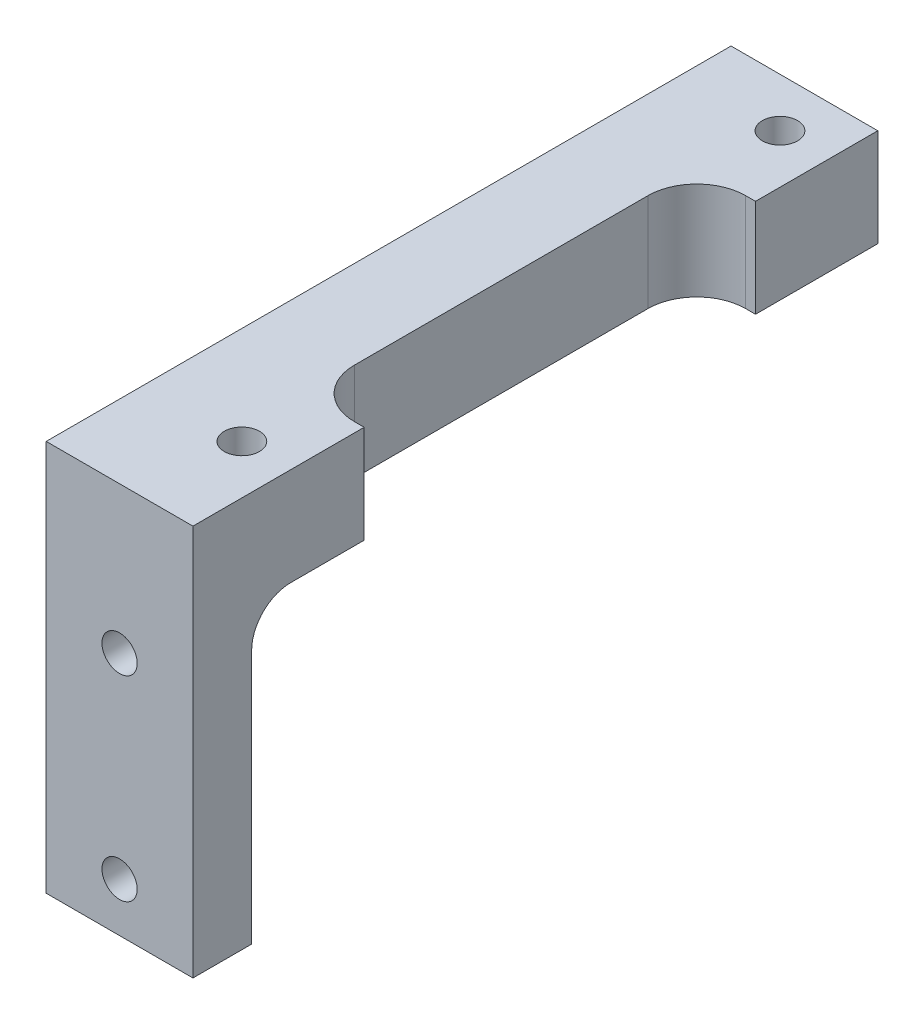
SolidWorks part; units mm, degrees
ref_plane "Front Plane" through (0, 0, 0) normal (0, 0, 1) x (1, 0, 0)
ref_plane "Top Plane" through (0, 0, 0) normal (0, 1, 0) x (1, 0, 0)
ref_plane "Right Plane" through (0, 0, 0) normal (1, 0, 0) x (0, 0, -1)
sketch "Sketch2" plane through (0, 0, 0) normal (0, 0, 1) x (1, 0, 0)
  line L1 (-23.8125, -12.7) -> (23.8125, -12.7)
  line L2 (-23.8125, -12.7) -> (-23.8125, 12.7)
  line L3 (-23.8125, 12.7) -> (23.8125, 12.7)
  line L4 (23.8125, -12.7) -> (23.8125, 12.7)
  line L5 (-23.8125, -12.7) -> (23.8125, 12.7) construction
  line L6 (-23.8125, 12.7) -> (23.8125, -12.7) construction
  point P0 (0, 0)
  dimension "D1" = 25.4
  dimension "D2" = 47.625
extrude "Boss-Extrude1" add sketch "Sketch2" along normal blind 44.45
sketch "Sketch3" plane through (0, 12.7, 0) normal (0, 1, 0) x (1, 0, 0)
  line L0 (0, 0) -> (0, -44.45) construction
  line L1 (23.8125, -44.45) -> (-23.8125, -44.45) construction
  line L2 (23.8125, 0) -> (-23.8125, 0) construction
  line L3 (-14.2875, -44.45) -> (14.2875, -44.45)
  line L4 (-14.2875, -44.45) -> (-14.2875, 0)
  line L5 (-14.2875, 0) -> (14.2875, 0)
  line L6 (14.2875, -44.45) -> (14.2875, 0)
  line L7 (-14.2875, -44.45) -> (14.2875, 0) construction
  line L8 (-14.2875, 0) -> (14.2875, -44.45) construction
  line L9 (23.8125, -44.45) -> (23.8125, 0) construction
  point P5 (0, -22.225)
  dimension "D1" = 9.525
extrude "Cut-Extrude1" cut sketch "Sketch3" against normal through all
sketch "Sketch4" plane through (-23.8125, 0, 0) normal (-1, 0, 0) x (0, 0, 1)
  line L0 (44.45, 12.7) -> (0, 12.7) construction
  line L1 (0, -12.7) -> (40.64, -12.7)
  line L2 (0, -12.7) -> (0, 6.35)
  line L3 (0, 6.35) -> (40.64, 6.35)
  line L4 (40.64, -12.7) -> (40.64, 6.35)
  line L5 (44.45, 12.7) -> (44.45, -12.7) construction
  dimension "D1" = 6.35
  dimension "D2" = 3.81
extrude "Cut-Extrude2" cut sketch "Sketch4" against normal through all
fillet "Fillet1" radius 2.54 1 edges at (19.05, 6.35, 40.64)
fillet "Fillet2" radius 2.54 1 edges at (-19.05, 6.35, 40.64)
sketch "Sketch5" plane through (0, 0, 44.45) normal (0, 0, 1) x (1, 0, 0)
  line L0 (-19.05, 12.7) -> (-19.05, -12.7) construction
  line L3 (-14.2875, 12.7) -> (-23.8125, 12.7) construction
  line L6 (-23.8125, -12.7) -> (-14.2875, -12.7) construction
  line L7 (19.05, -12.7) -> (19.05, 12.7) construction
  line L8 (14.2875, -12.7) -> (23.8125, -12.7) construction
  line L9 (23.8125, 12.7) -> (14.2875, 12.7) construction
  circle A2 centre (-19.05, -9.525) radius 1.143
  circle A3 centre (-19.05, 3.175) radius 1.143
  circle A4 centre (19.05, -9.525) radius 1.143
  circle A5 centre (19.05, 3.175) radius 1.143
  dimension "D1" = 2.286
  dimension "D2" = 2.286
  dimension "D3" = 12.7
  dimension "D4" = 3.175
  dimension "D5" = 12.7
  dimension "D6" = 3.175
  dimension "D7" = 2.286
  dimension "D8" = 2.286
extrude "Cut-Extrude3" cut sketch "Sketch5" against normal through all
sketch "Sketch6" plane through (0, 0, 44.45) normal (0, 0, 1) x (1, 0, 0)
  line L0 (19.05, -12.7) -> (19.05, 12.7) construction
  line L1 (14.2875, -12.7) -> (23.8125, -12.7) construction
  line L2 (23.8125, 12.7) -> (14.2875, 12.7) construction
  circle A1 centre (19.05, -9.525) radius 1.143
  circle A2 centre (19.05, 3.175) radius 1.143
  dimension "D1" = 12.7
  dimension "D2" = 3.175
  dimension "D3" = 2.286
  dimension "D4" = 2.286
extrude "Cut-Extrude4" cut sketch "Sketch6" against normal through all
sketch "Sketch7" plane through (0, 12.7, 0) normal (0, 1, 0) x (1, 0, 0)
  line L0 (0, 0) -> (0, -46.99) construction
  line L1 (-14.2875, 0) -> (-23.8125, 0) construction
  line L2 (-17.4625, -38.1) -> (17.4625, -38.1) construction
  line L3 (-17.4625, -38.1) -> (-17.4625, -3.175) construction
  line L4 (-17.4625, -3.175) -> (17.4625, -3.175) construction
  line L5 (17.4625, -38.1) -> (17.4625, -3.175) construction
  line L6 (-17.4625, -38.1) -> (17.4625, -3.175) construction
  line L7 (-17.4625, -3.175) -> (17.4625, -38.1) construction
  circle A1 centre (-17.4625, -38.1) radius 1.143
  circle A2 centre (17.4625, -38.1) radius 1.143
  circle A3 centre (-17.4625, -3.175) radius 1.143
  circle A4 centre (17.4625, -3.175) radius 1.143
  point P11 (0, -20.6375)
  dimension "D4" = 2.286
  dimension "D5" = 2.286
  dimension "D6" = 2.286
  dimension "D7" = 2.286
  dimension "D1" = 34.925
  dimension "D2" = 34.925
  dimension "D3" = 3.175
extrude "Cut-Extrude5" cut sketch "Sketch7" against normal blind 10.16
sketch "Sketch8" plane through (0, 12.7, 0) normal (0, 1, 0) x (1, 0, 0)
  line L0 (0, 0) -> (0, -46.99) construction
  line L1 (-17.4625, -20.6375) -> (17.4625, -20.6375) construction
  line L2 (-17.4625, -3.175) -> (17.4625, -3.175) construction
  line L3 (-17.4625, -3.175) -> (-17.4625, -38.1) construction
  line L4 (-17.4625, -38.1) -> (17.4625, -38.1) construction
  line L5 (17.4625, -3.175) -> (17.4625, -38.1) construction
  line L6 (-14.2875, 0) -> (-14.2875, -44.45) construction
  line L7 (-18.0975, -33.3375) -> (18.0975, -33.3375)
  line L8 (-18.0975, -33.3375) -> (-18.0975, -7.9375)
  line L9 (-18.0975, -7.9375) -> (18.0975, -7.9375)
  line L10 (18.0975, -33.3375) -> (18.0975, -7.9375)
  line L11 (-18.0975, -33.3375) -> (18.0975, -7.9375) construction
  line L12 (-18.0975, -7.9375) -> (18.0975, -33.3375) construction
  point P11 (0, -20.6375)
  dimension "D1" = 3.81
  dimension "D2" = 25.4
extrude "Cut-Extrude6" cut sketch "Sketch8" against normal through all
fillet "Fillet3" radius 3.175 2 edges at (-18.0975, 9.525, 7.9375) (-18.0975, 9.525, 33.3375)
fillet "Fillet4" radius 3.175 2 edges at (18.0975, 9.525, 7.9375) (18.0975, 9.525, 33.3375)
sketch "Sketch9" plane through (0, 0, 0) normal (1, 0, 0) x (0, 0, -1)
  line L1 (-68.2457, 26.7867) -> (19.6669, 26.7867)
  line L2 (-68.2457, 26.7867) -> (-68.2457, -26.9881)
  line L3 (-68.2457, -26.9881) -> (19.6669, -26.9881)
  line L4 (19.6669, 26.7867) -> (19.6669, -26.9881)
extrude "Cut-Extrude7" cut sketch "Sketch9" along normal blind 35.56
